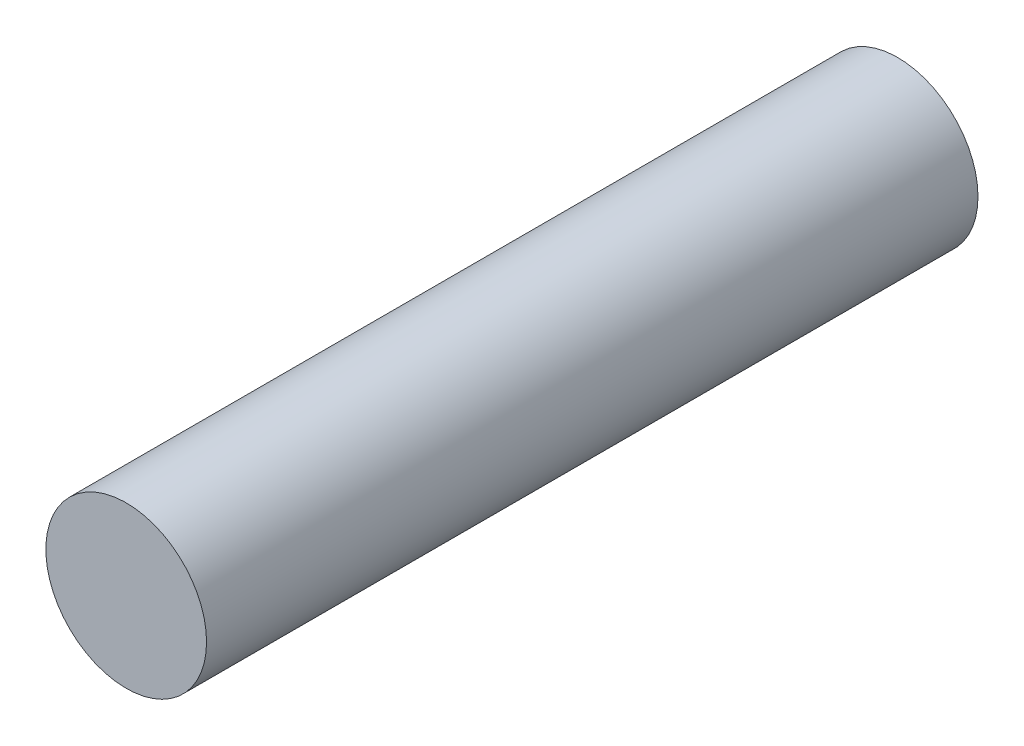
SolidWorks part; units mm, degrees
ref_plane "Front Plane" through (0, 0, 0) normal (0, 0, 1) x (1, 0, 0)
ref_plane "Top Plane" through (0, 0, 0) normal (0, 1, 0) x (1, 0, 0)
ref_plane "Right Plane" through (0, 0, 0) normal (1, 0, 0) x (0, 0, -1)
sketch "Sketch1" plane through (0, 0, 0) normal (0, 0, 1) x (1, 0, 0)
  circle A0 centre (0, 0) radius 7.5
  dimension "D1" = 15
extrude "Boss-Extrude1" add sketch "Sketch1" along normal blind 72
